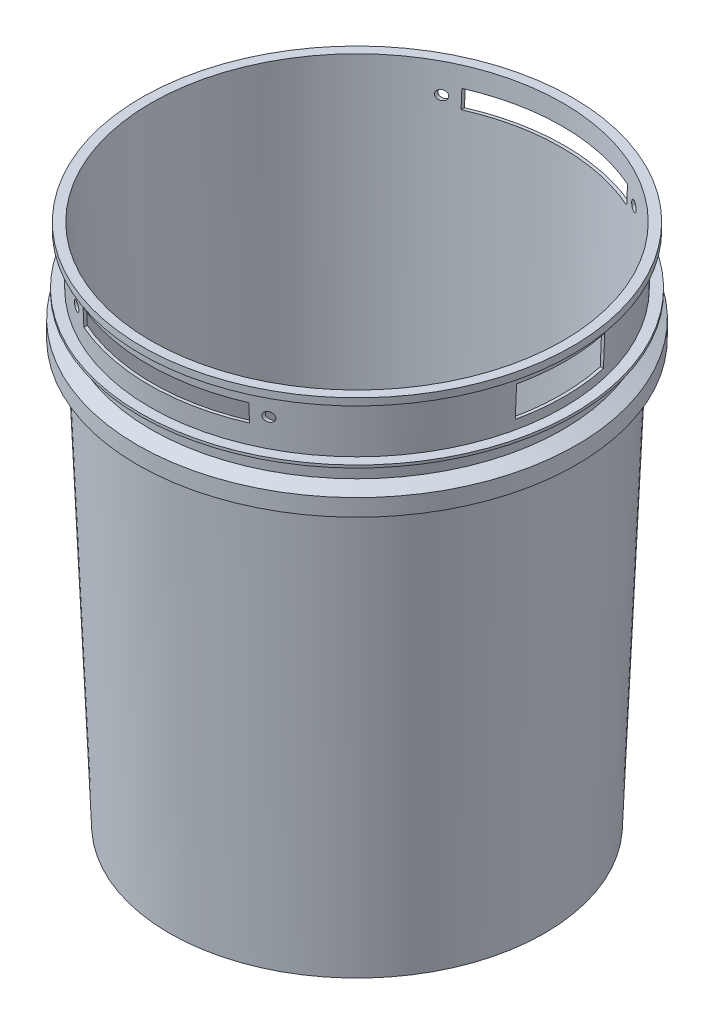
SolidWorks part; units mm, degrees
ref_plane "Front Plane" through (0, 0, 0) normal (0, 0, 1) x (1, 0, 0)
ref_plane "Top Plane" through (0, 0, 0) normal (0, 1, 0) x (1, 0, 0)
ref_plane "Right Plane" through (0, 0, 0) normal (1, 0, 0) x (0, 0, -1)
sketch "Sketch1" plane through (0, 0, 0) normal (0, 0, 1) x (1, 0, 0)
  line L0 (0, 0) -> (0, 368.3)
  line L1 (0, 368.3) -> (145.2562, 368.3)
  line L2 (145.2562, 368.3) -> (130.175, 0)
  line L3 (130.175, 0) -> (0, 0)
  line L4 (147.4563, 368.3) -> (151.9563, 368.3)
  line L5 (151.9563, 368.3) -> (151.9563, 363.3)
  line L6 (150.9563, 363.3) -> (151.9563, 363.3)
  line L7 (130.175, 0) -> (132.375, 0)
  line L8 (132.375, 0) -> (147.4563, 368.3)
  line L9 (145.2562, 368.3) -> (147.4563, 368.3)
  line L10 (147.4153, 367.3) -> (150.9563, 367.3)
  line L11 (150.9563, 367.3) -> (150.9563, 363.3)
  line L12 (150.9563, 367.3) -> (150.9563, 364.3) construction
  line L13 (150.9563, 364.3) -> (145.0515, 364.3) construction
  line L14 (151.9563, 363.3) -> (145.0515, 363.3) construction
  line L15 (0, 2) -> (132.4569, 2)
  line L16 (147.4563, 367.3) -> (150.9563, 367.3) construction
  line L17 (145.8025, 327.913) -> (152.8971, 327.913)
  line L18 (152.8971, 327.913) -> (152.8971, 326.073)
  line L19 (152.8971, 326.073) -> (145.7271, 326.073)
  line L20 (145.2362, 314.0831) -> (154.8009, 309.3471)
  line L21 (154.8009, 309.3471) -> (154.8009, 297.3471)
  line L22 (154.8009, 297.3471) -> (144.5509, 297.3471)
  line L23 (145.1802, 312.7159) -> (153.5509, 308.5712)
  line L24 (153.5509, 308.5712) -> (153.5509, 297.3471)
  line L25 (153.5509, 308.5712) -> (153.5509, 298.5971) construction
  line L26 (153.5509, 298.5971) -> (144.5509, 298.5971) construction
  line L28 (144.6815, 312.9629) -> (153.5509, 308.5712) construction
  dimension "D1" = 130.175
  dimension "D2" = 145.2562
  dimension "D3" = 6.7
  dimension "D4" = 368.3
  dimension "D5" = 4.5
  dimension "D6" = 5
  dimension "D7" = 1
  dimension "D8" = 2
  dimension "D9" = 1.84
  dimension "D10" = 39.42
  dimension "D11" = 7.17
  dimension "D12" = 12
  dimension "D13" = 16.75
  dimension "D14" = 12
  dimension "D15" = 10.25
  dimension "D16" = 1.25
ref_axis "Axis1" through (0, 0, 0) along (0, 1, 0)
revolve "Revolve1" add sketch "Sketch1" angle 360 about axis through (0, 0, 0) along (0, 1, 0)
sketch "Sketch2" plane through (0, 0, 0) normal (0, 0, 1) x (1, 0, 0)
  line L0 (0, 368.3) -> (0, 327.913) construction
  line L1 (-58.42, 354.4565) -> (58.42, 354.4565)
  line L2 (-58.42, 354.4565) -> (-58.42, 341.7565)
  line L3 (-58.42, 341.7565) -> (58.42, 341.7565)
  line L4 (58.42, 354.4565) -> (58.42, 341.7565)
  line L5 (145.2562, 368.3) -> (-145.2562, 368.3) construction
  line L6 (152.8971, 327.913) -> (-152.8971, 327.913) construction
  line L7 (-67.82, 348.1065) -> (67.82, 348.1065) construction
  circle A0 centre (67.82, 348.1065) radius 3.302
  circle A1 centre (-67.82, 348.1065) radius 3.302
  point P8 (0, 348.1065)
  point P9 (0, 348.1065)
  dimension "D3" = 6.604
  dimension "D1" = 116.84
  dimension "D2" = 12.7
  dimension "D4" = 135.64
extrude "Cut-Extrude1" cut sketch "Sketch2" along normal mid plane 355.6
sketch "Sketch3" plane through (0, 0, 0) normal (1, 0, 0) x (0, 0, -1)
  line L0 (0, 363.3243) -> (0, 327.913) construction
  line L1 (31.1, 356.6687) -> (-31.1, 356.6687)
  line L2 (31.1, 356.6687) -> (31.1, 334.5687)
  line L3 (31.1, 334.5687) -> (-31.1, 334.5687)
  line L4 (-31.1, 356.6687) -> (-31.1, 334.5687)
  line L8 (152.8971, 327.913) -> (-152.8971, 327.913) construction
  line L9 (0, 345.6187) -> (31.1, 345.6187) construction
  dimension "D1" = 62.2
  dimension "D2" = 22.1
extrude "Cut-Extrude2" cut sketch "Sketch3" along normal up to surface (143.652 mm away)
